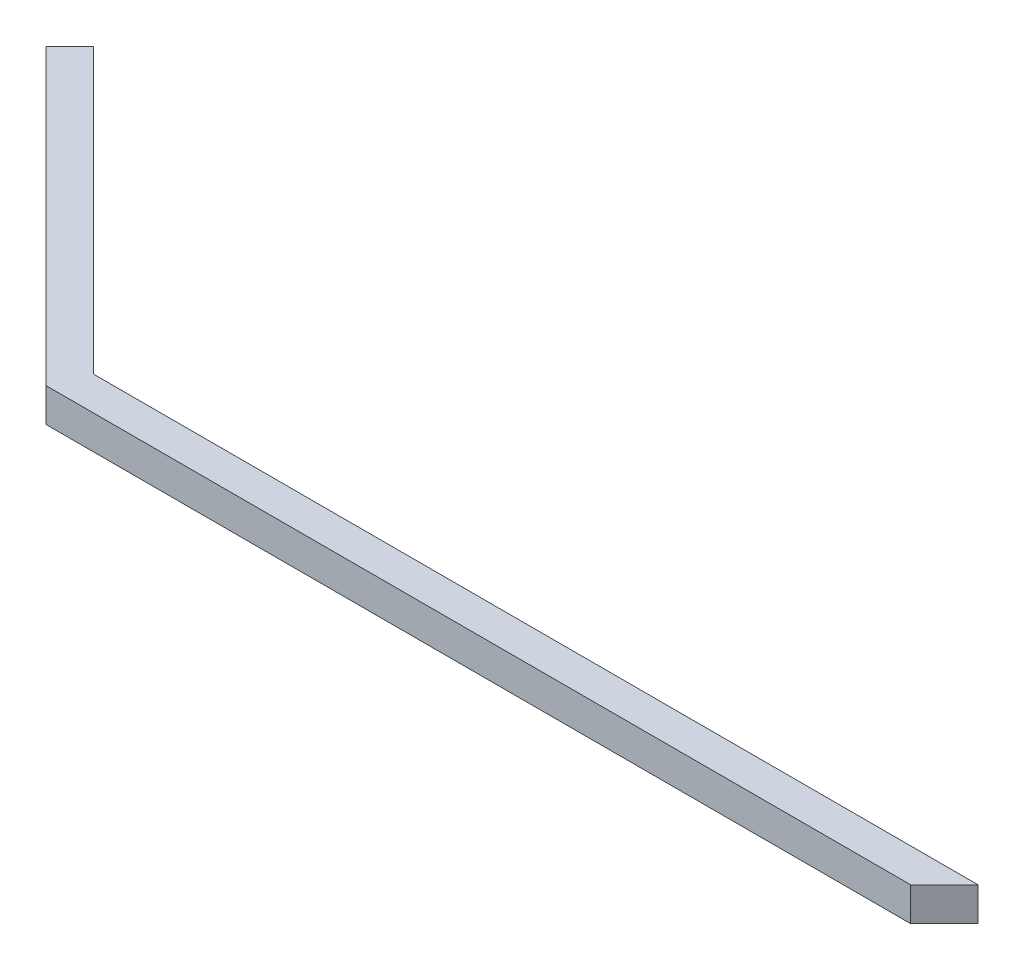
SolidWorks part; units mm, degrees
ref_plane "Front Plane" through (0, 0, 0) normal (0, 0, 1) x (1, 0, 0)
ref_plane "Top Plane" through (0, 0, 0) normal (0, 1, 0) x (1, 0, 0)
ref_plane "Right Plane" through (0, 0, 0) normal (1, 0, 0) x (0, 0, -1)
sketch "Sketch1" plane through (0, 0, 0) normal (0, 1, 0) x (1, 0, 0)
  line L0 (-131.7487, 50.6173) -> (-117.6066, 64.7594) construction
  line L1 (-117.6066, 64.7594) -> (-124.6777, 57.6883) construction
  line L2 (-124.6777, 57.6883) -> (-98.9541, 31.9647) construction
  line L3 (-98.9541, 31.9647) -> (-21.0754, 31.9647) construction
  line L4 (-125.7383, 56.6277) -> (-99.5754, 30.4647)
  line L5 (-99.5754, 30.4647) -> (-22.5754, 30.4647)
  line L6 (-123.617, 58.749) -> (-98.3327, 33.4647)
  line L7 (-98.3327, 33.4647) -> (-22.5754, 33.4647)
  line L8 (-125.7383, 56.6277) -> (-123.617, 58.749)
  line L10 (-19.5754, 33.4647) -> (-22.5754, 30.4647)
  line L11 (-98.3327, 33.4647) -> (-19.5754, 33.4647) construction
  line L12 (-98.9541, 31.9647) -> (-19.5754, 31.9647) construction
  line L13 (-22.5754, 33.4647) -> (-19.5754, 33.4647)
  line L14 (-99.5754, 30.4647) -> (-19.5754, 30.4647) construction
  dimension "D1" = 1.5
  dimension "D2" = 1.5
  dimension "D3" = 135
  dimension "D4" = 37
  dimension "D5" = 77
extrude "Boss-Extrude1" add sketch "Sketch1" along normal blind 3
